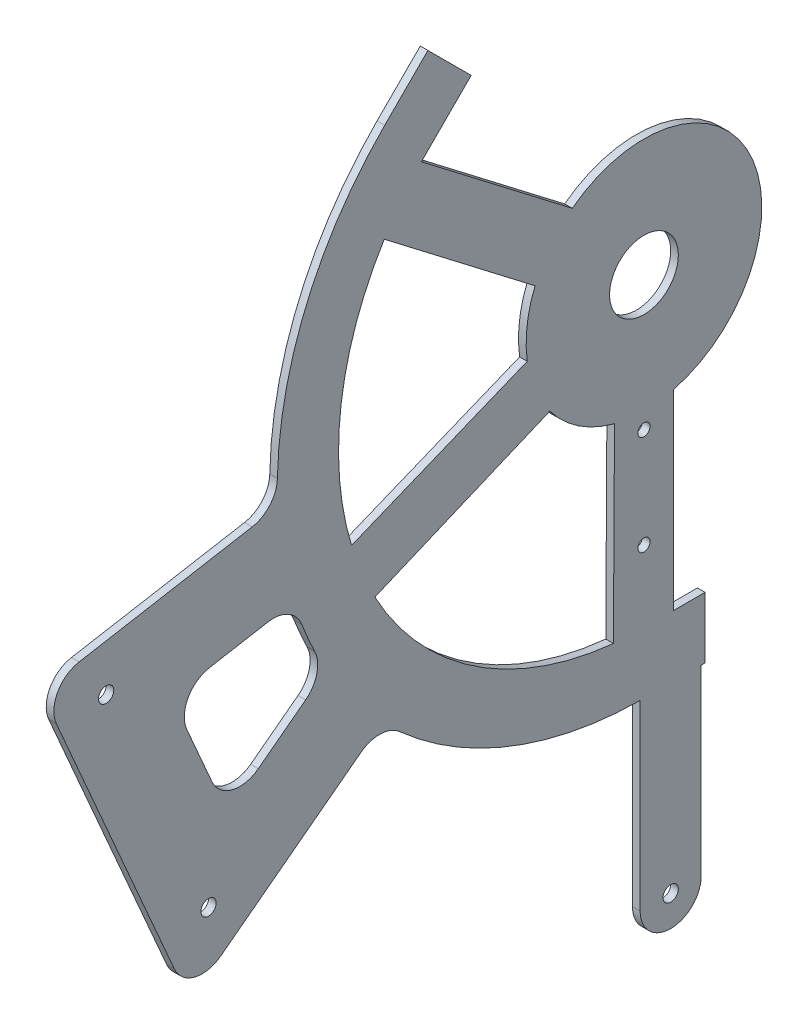
SolidWorks part; units mm, degrees
ref_plane "Front Plane" through (0, 0, 0) normal (0, 0, 1) x (1, 0, 0)
ref_plane "Top Plane" through (0, 0, 0) normal (0, 1, 0) x (1, 0, 0)
ref_plane "Right Plane" through (0, 0, 0) normal (1, 0, 0) x (0, 0, -1)
sketch "Sketch8" plane through (0, 0, 0) normal (1, 0, 0) x (0, 0, -1)
  line L0 (0, 0) -> (-139.7, 0) construction
  circle A1 centre (-272.2355, -114.6296) radius 12.7
  circle A3 centre (-223.5488, -39.2772) radius 3.175
  circle A5 centre (-180.9898, -137.1562) radius 3.175
  circle A7 centre (0, 0) radius 12.7
  circle A9 centre (11.1033, -228.1813) radius 3.175
  circle A10 centre (0, 0) radius 336.7856
  circle A11 centre (0, 0) radius 127
  circle A12 centre (0, 0) radius 152.4
sketch "Sketch9" plane through (0, 0, 0) normal (1, 0, 0) x (0, 0, -1)
  line L0 (0, -126.9544) -> (0, -152.3905)
  line L1 (-89.7703, 89.7703) -> (-107.7564, 107.7564) construction
  line L2 (-98.7633, 98.7633) -> (-80.8028, 116.7239) construction
  line L3 (-107.7564, 107.7564) -> (-89.7959, 125.7169)
  line L4 (-89.7959, 125.7169) -> (-71.8098, 107.7308)
  line L5 (-71.8098, 107.7308) -> (-89.7703, 89.7703)
  arc A0 (-107.7564, 107.7564) -> (0, -152.3905) centre (0, 0) ccw
  arc A1 (-89.7703, 89.7703) -> (0, -126.9544) centre (0, 0) ccw
  dimension "D1" = 25.4
extrude "Boss-Extrude2" add sketch "Sketch9" along normal blind 3.175
sketch "Sketch11" plane through (0, 0, 0) normal (1, 0, 0) x (0, 0, -1)
  line L0 (0, -152.3905) -> (0, -126.9544) construction
  line L1 (0, -152.3905) -> (0, -126.9544)
  line L2 (0, -126.9544) -> (25.4, -126.9544)
  line L3 (25.4, -126.9544) -> (25.4, -152.3905)
  line L4 (25.4, -152.3905) -> (0, -152.3905)
  dimension "D1" = 25.4
extrude "Boss-Extrude4" add sketch "Sketch11" along normal blind 3.175
sketch "Sketch12" plane through (0, 0, 0) normal (1, 0, 0) x (0, 0, -1)
  line L0 (11.1033, -228.1813) -> (11.1033, -152.3905) construction
  line L1 (0, -152.3905) -> (25.4, -152.3905) construction
  line L2 (23.8033, -228.1813) -> (23.8033, -152.3905)
  line L3 (-1.5967, -228.1813) -> (-1.5967, -152.3822)
  line L4 (0, -152.3905) -> (23.8033, -152.3905)
  line L5 (-1.5967, -228.1813) -> (-1.5967, -152.3905) construction
  circle A0 centre (11.1033, -228.1813) radius 3.175 construction
  circle A1 centre (11.1033, -228.1813) radius 3.175
  arc A2 (-107.7564, 107.7564) -> (0, -152.3905) centre (0, 0) ccw construction
  arc A3 (-1.5967, -152.3822) -> (0, -152.3905) centre (0, 0) ccw
  arc A4 (23.8033, -228.1813) -> (-1.5717, -227.3844) centre (11.1033, -228.1813) cw
extrude "Boss-Extrude5" add sketch "Sketch12" along normal blind 3.175
sketch "Sketch13" plane through (0, 0, 0) normal (1, 0, 0) x (0, 0, -1)
  line L0 (-223.5488, -39.2772) -> (0, 0) construction
  line L1 (-180.9898, -137.1562) -> (0, 0) construction
  line L2 (-180.9898, -137.1562) -> (-223.5488, -39.2772) construction
  line L3 (-175.9217, -157.2176) -> (-117.6154, -113.0324)
  line L4 (-234.7837, -21.9094) -> (-162.8611, -9.2727)
  line L5 (-195.2389, -152.1598) -> (-244.2327, -39.4819)
  line L6 (-160.3069, -97.5804) -> (-140.627, -82.6667)
  line L7 (-180.5603, -51.066) -> (-156.268, -46.7979)
  line L8 (-179.6241, -92.5226) -> (-190.0092, -68.6385)
  line L9 (-250.6605, -24.6989) -> (74.2878, 32.3941) construction
  line L10 (-188.7972, -166.9748) -> (74.2878, 32.3941) construction
  line L11 (-173.1824, -107.3376) -> (-74.2878, -32.3941) construction
  line L12 (-196.437, -53.8555) -> (-74.2878, -32.3941) construction
  line L13 (-173.1824, -107.3376) -> (-196.437, -53.8555) construction
  line L14 (-188.7972, -166.9748) -> (-250.6605, -24.6989) construction
  circle A0 centre (-180.9898, -137.1562) radius 3.175 construction
  circle A2 centre (-223.5488, -39.2772) radius 3.175 construction
  circle A3 centre (-180.9898, -137.1562) radius 3.175
  circle A5 centre (-223.5488, -39.2772) radius 3.175
  arc A9 (-180.5603, -51.066) -> (-190.0092, -68.6385) centre (-178.3625, -63.5744) ccw
  arc A10 (-160.3069, -97.5804) -> (-179.6241, -92.5226) centre (-167.9775, -87.4585) cw
  arc A11 (-175.9217, -157.2176) -> (-195.2389, -152.1598) centre (-183.5923, -147.0957) cw
  arc A12 (-234.7837, -21.9094) -> (-244.2327, -39.4819) centre (-232.586, -34.4178) ccw
  arc A13 (-152.3613, 2.9868) -> (-142.218, -54.744) centre (0, 0) ccw
  arc A14 (-136.8893, -66.9641) -> (-101.4871, -113.6804) centre (0, 0) ccw
  arc A15 (-117.6154, -113.0324) -> (-101.4871, -113.6804) centre (-109.9449, -123.1544) cw
  arc A16 (-140.627, -82.6667) -> (-136.8893, -66.9641) centre (-148.2975, -72.5448) ccw
  arc A17 (-156.268, -46.7979) -> (-142.218, -54.744) centre (-154.0703, -59.3063) cw
  arc A18 (-162.8611, -9.2727) -> (-152.3613, 2.9868) centre (-165.0588, 3.2357) ccw
  dimension "D1" = 12.7
  dimension "D2" = 12.7
extrude "Boss-Extrude6" add sketch "Sketch13" along normal blind 3.175
sketch "Sketch14" plane through (0, 0, 0) normal (1, 0, 0) x (0, 0, -1)
  line L0 (0, 0) -> (-117.2906, -48.5833) construction
  line L1 (0, 0) -> (0, -126.9544) construction
  line L2 (0, 0) -> (-84.3977, 64.7606) construction
  line L3 (-29.7998, 38.8742) -> (-100.3289, 92.9931)
  line L4 (25.4, -126.9544) -> (0, -126.9544) construction
  line L5 (12.2455, -126.9544) -> (0, -126.9544)
  line L6 (-84.3977, 64.7606) -> (-92.129, 54.6851) construction
  line L8 (12.2455, -47.4265) -> (12.2455, -126.9544)
  line L9 (-84.3977, 64.7606) -> (-76.6664, 74.8362) construction
  line L10 (-12.2455, -47.4265) -> (-12.7, -126.3176)
  line L11 (-100.3289, 92.9931) -> (-115.7914, 72.8419)
  line L12 (-39.1303, -29.4627) -> (-111.8421, -60.0729)
  line L14 (-48.5025, -6.836) -> (-121.5623, -36.6064)
  line L16 (-45.2623, 18.723) -> (-115.7914, 72.8419)
  circle A1 centre (0, 0) radius 14.2875
  arc A2 (-89.7703, 89.7703) -> (0, -126.9544) centre (0, 0) ccw construction
  arc A3 (-39.1303, -29.4627) -> (-12.2455, -47.4265) centre (0, 0) ccw
  arc A4 (12.2455, -47.4265) -> (-29.7998, 38.8742) centre (0, 0) ccw
  arc A5 (-45.2623, 18.723) -> (-48.5025, -6.836) centre (0, 0) ccw
  arc A7 (-121.5623, -36.6064) -> (-111.8421, -60.0729) centre (0, 0) ccw
  arc A8 (-12.7, -126.3176) -> (0, -126.9544) centre (0, 0) ccw
  dimension "D1" = 12.7
  dimension "D4" = 28.575
  dimension "D2" = 88.9
  dimension "D3" = 60
extrude "Boss-Extrude7" add sketch "Sketch14" along normal blind 3.175
sketch "Sketch15" plane through (3.175, 0, 0) normal (1, 0, 0) x (0, 0, -1)
  line L6 (0, -14.2875) -> (0, -55.7419) construction
  line L7 (0, -55.7419) -> (0, -97.1963) construction
  line L8 (0, -97.1963) -> (0, -138.6507) construction
  circle A0 centre (0, 0) radius 14.2875 construction
  circle A2 centre (11.1033, -228.1813) radius 3.175 construction
  circle A3 centre (11.1033, -228.1813) radius 3.175
  circle A4 centre (0, -55.7419) radius 2.54
  circle A5 centre (0, -97.1963) radius 2.54
extrude "Cut-Extrude1" cut sketch "Sketch15" against normal through all
